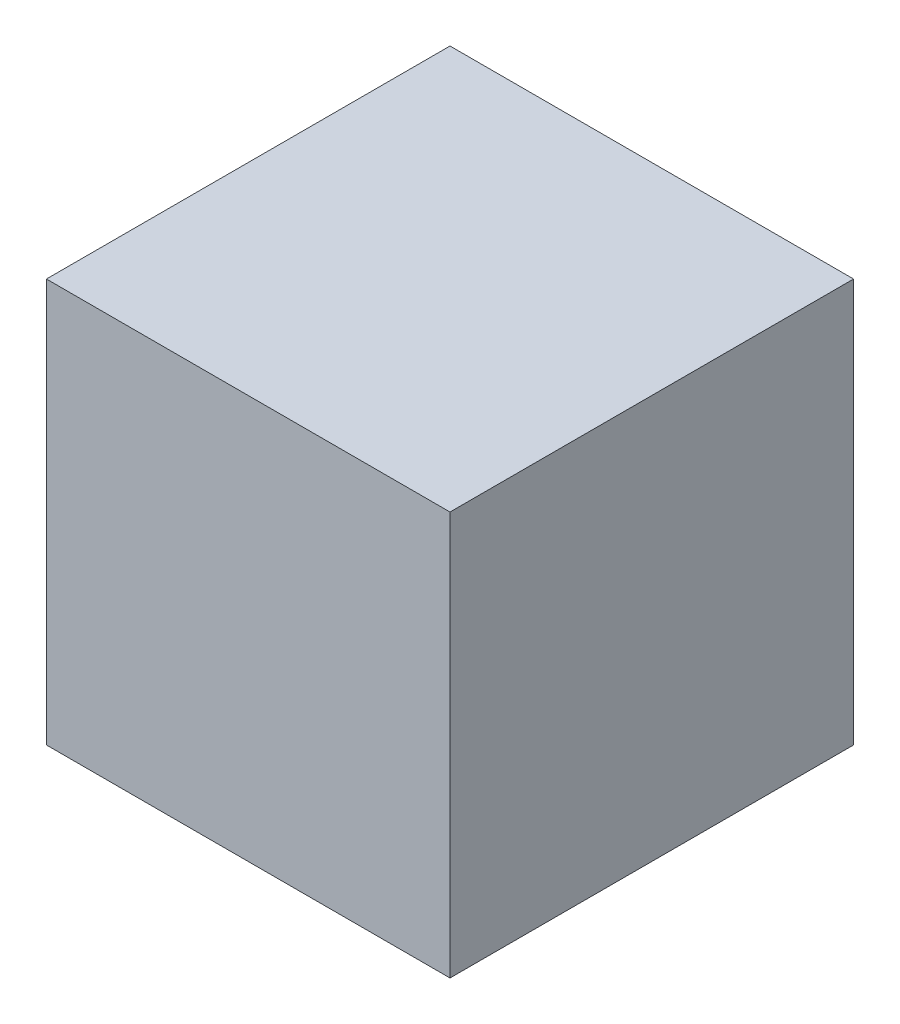
SolidWorks part; units mm, degrees
ref_plane "Plan de face" through (0, 0, 0) normal (0, 0, 1) x (1, 0, 0)
ref_plane "Plan de dessus" through (0, 0, 0) normal (0, 1, 0) x (1, 0, 0)
ref_plane "Plan de droite" through (0, 0, 0) normal (1, 0, 0) x (0, 0, -1)
sketch "Esquisse1" plane through (0, 0, 0) normal (0, 0, 1) x (1, 0, 0)
  line L1 (0, 0) -> (58, 0)
  line L2 (0, 0) -> (0, 58)
  line L3 (0, 58) -> (58, 58)
  line L4 (58, 0) -> (58, 58)
  dimension "D1" = 58
  dimension "D2" = 58
extrude "Boss.-Extru.1" add sketch "Esquisse1" along normal blind 58
